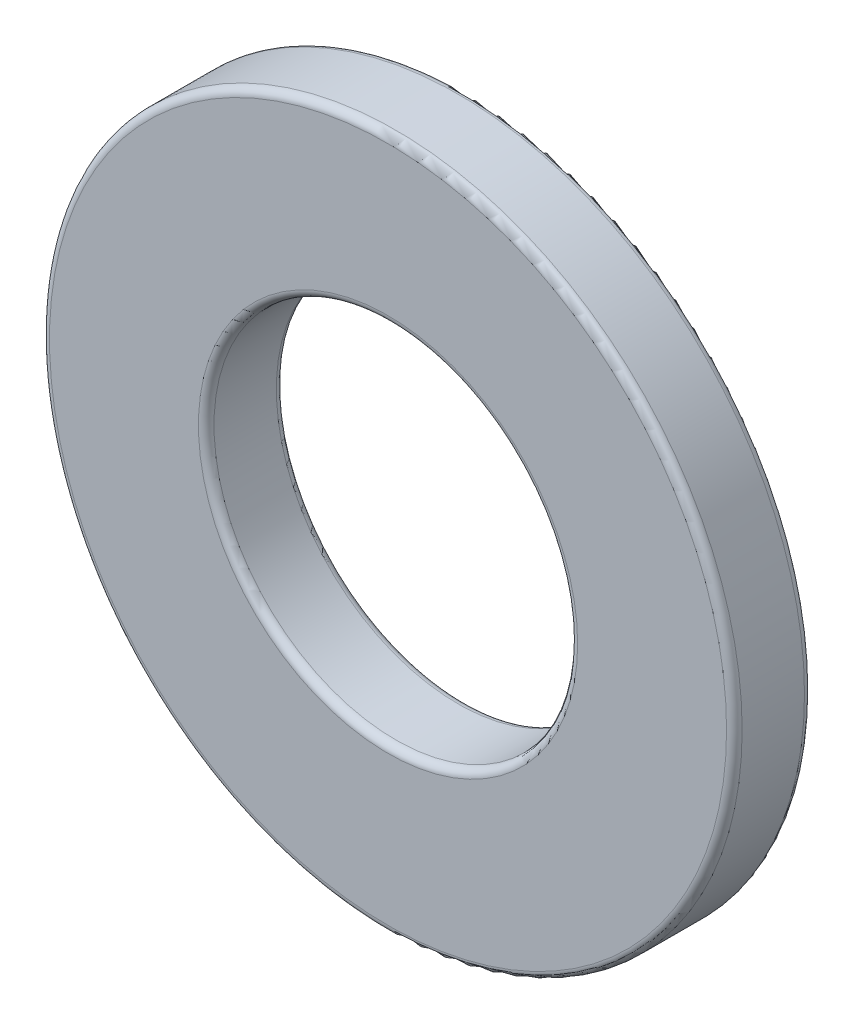
SolidWorks part; units mm, degrees
ref_plane "Front Plane" through (0, 0, 0) normal (0, 0, 1) x (1, 0, 0)
ref_plane "Top Plane" through (0, 0, 0) normal (0, 1, 0) x (1, 0, 0)
ref_plane "Right Plane" through (0, 0, 0) normal (1, 0, 0) x (0, 0, -1)
sketch "Sketch1" plane through (0, 0, 0) normal (0, 0, 1) x (1, 0, 0)
  circle A0 centre (0, 0) radius 8 construction
  circle A1 centre (0, 0) radius 4.2 construction
  dimension "OD" = 16
  dimension "ID" = 8.4
sketch "Sketch2" plane through (0, 0, 0) normal (1, 0, 0) x (0, 0, -1)
  line L0 (-0.9, -8) -> (0.9, -8) construction
  point P0 (0.5, -8)
  point P4 (0, -8)
  dimension "Thickness Max" = 1.8
  dimension "Thickness Min" = 1.4
sketch "Sketch3" plane through (0, 0, 0) normal (0, 0, 1) x (1, 0, 0)
  circle A0 centre (0, 0) radius 8 construction
  circle A1 centre (0, 0) radius 8
  circle A2 centre (0, 0) radius 4.2 construction
  circle A3 centre (0, 0) radius 4.2
extrude "Boss-Extrude1" add sketch "Sketch3" against normal up to vertex (0.9 mm away) and the other way up to vertex (0.9 mm away) up to point (0, -8, -0.9) other way up to point (0, -8, 0.9)
fillet "Fillet1" radius 0.18 4 edges at (8, 0, -0.9) (4.2, 0, -0.9) (4.2, 0, 0.9) (8, 0, 0.9)
equation "\"D1@Fillet1\" = \"Thickness Max@Sketch2\" * 0.1"
